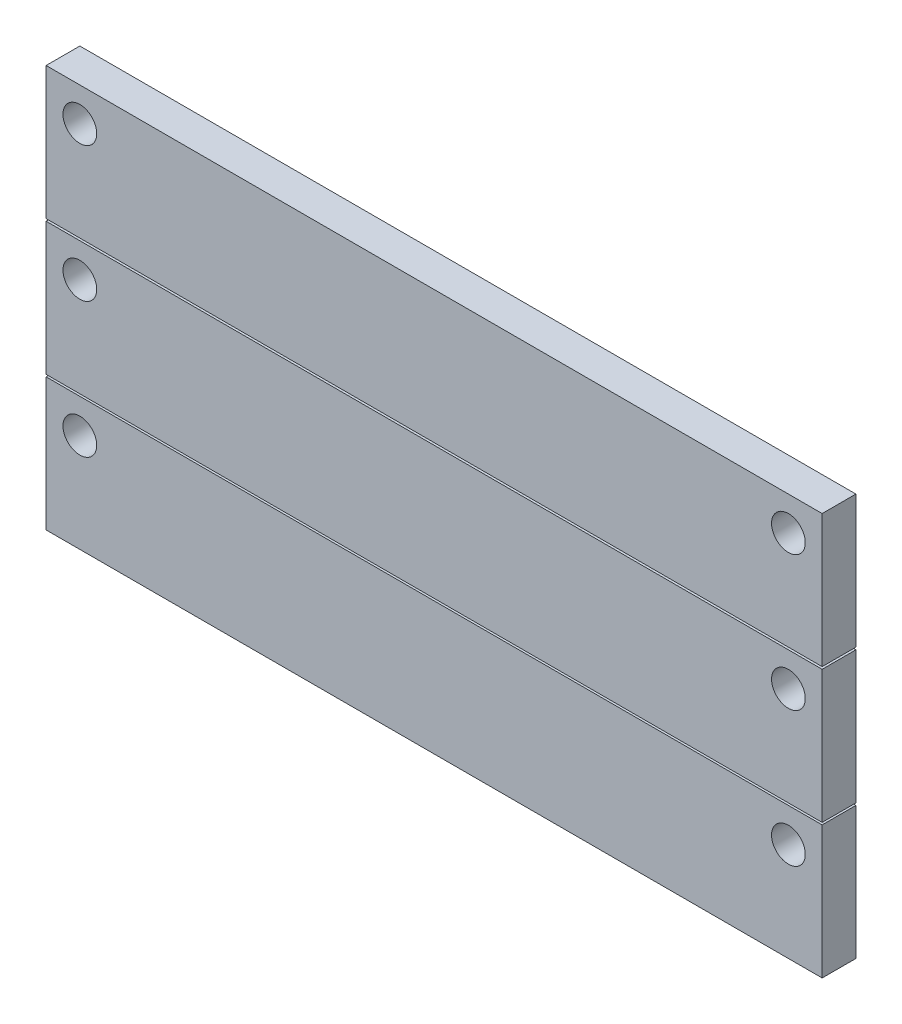
SolidWorks part; units mm, degrees
ref_plane "Front Plane" through (0, 0, 0) normal (0, 0, 1) x (1, 0, 0)
ref_plane "Top Plane" through (0, 0, 0) normal (0, 1, 0) x (1, 0, 0)
ref_plane "Right Plane" through (0, 0, 0) normal (1, 0, 0) x (0, 0, -1)
sketch "Sketch1" plane through (0, 0, 0) normal (0, 0, 1) x (1, 0, 0)
  line L0 (0, 0) -> (-584.2, 0)
  line L1 (-584.2, 0) -> (-584.2, -99.822)
  line L2 (-584.2, -99.822) -> (0, -99.822)
  line L3 (0, -99.822) -> (0, 0)
  line L4 (0, 101.5397) -> (-584.2, 101.5397)
  line L5 (-584.2, 101.5397) -> (-584.2, 1.7177)
  line L6 (-584.2, 1.7177) -> (0, 1.7177)
  line L7 (0, 1.7177) -> (0, 101.5397)
  line L12 (0, -101.4458) -> (-584.2, -101.4458)
  line L13 (-584.2, -101.4458) -> (-584.2, -201.2678)
  line L14 (-584.2, -201.2678) -> (0, -201.2678)
  line L15 (0, -201.2678) -> (0, -101.4458)
  dimension "D1" = 90
  dimension "D2" = 584.2
  dimension "D3" = 99.822
extrude "Boss-Extrude1" add sketch "Sketch1" along normal blind 25.4
sketch "Sketch2" plane through (0, 0, 25.4) normal (0, 0, 1) x (1, 0, 0)
  line L0 (-584.2, 0) -> (-584.2, -99.822) construction
  line L2 (-292.1, 101.5397) -> (-292.1, -298.1217) construction
  line L3 (0, 101.5397) -> (-584.2, 101.5397) construction
  circle A0 centre (-558.8, 76.1397) radius 12.7
  circle A1 centre (-25.4, 76.1397) radius 12.7
  dimension "D1" = 25.4
  dimension "D2" = 25.4
  dimension "D3" = 25.4
extrude "Cut-Extrude1" cut sketch "Sketch2" against normal through all
pattern_linear "LPattern1" count 3 spacing 101.6 along (0, -1, 0) of "Cut-Extrude1"
